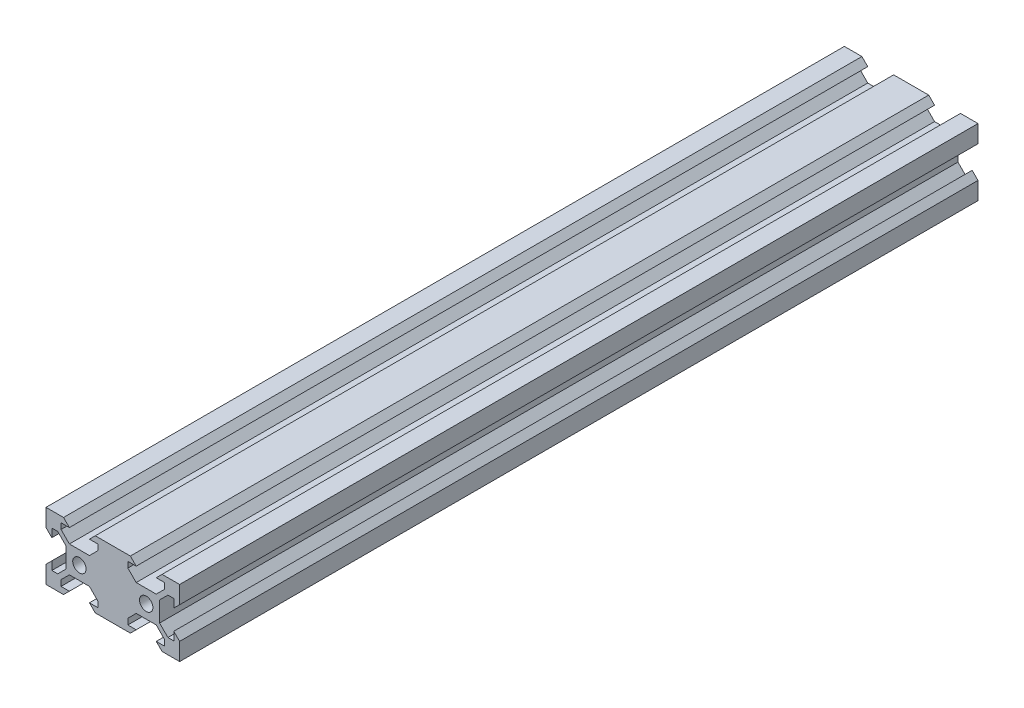
SolidWorks part; units mm, degrees
ref_plane "Alzado" through (0, 0, 0) normal (0, 0, 1) x (1, 0, 0)
ref_plane "Planta" through (0, 0, 0) normal (0, 1, 0) x (1, 0, 0)
ref_plane "Vista lateral" through (0, 0, 0) normal (1, 0, 0) x (0, 0, -1)
sketch "Croquis1" plane through (0, 0, 0) normal (0, 0, 1) x (1, 0, 0)
  line L0 (0, 10) -> (0, 4) construction
  line L1 (-10, 10) -> (10, 10)
  line L2 (-10, 10) -> (-10, -10)
  line L3 (-10, -10) -> (30, -10)
  line L4 (10, 10) -> (10, -10)
  line L5 (-10, 10) -> (10, -10) construction
  line L6 (-10, -10) -> (10, 10) construction
  line L7 (-3, 4) -> (3, 4)
  line L8 (4.75, 10) -> (3, 8.25)
  line L9 (3, 8.25) -> (5.5, 8.25)
  line L10 (5.5, 8.25) -> (5.5, 6.5)
  line L11 (5.5, 6.5) -> (3, 4)
  line L12 (4.75, 10) -> (-4.75, 10)
  line L13 (0, 10) -> (0, 4) construction
  line L14 (-4.75, 10) -> (-3, 8.25)
  line L15 (-3, 8.25) -> (-5.5, 8.25)
  line L16 (-5.5, 8.25) -> (-5.5, 6.5)
  line L17 (-5.5, 6.5) -> (-3, 4)
  line L18 (20, 10) -> (20, 4) construction
  line L19 (10, -4.75) -> (10, 4.75)
  line L20 (10, 4.75) -> (8.25, 3)
  line L21 (8.25, 3) -> (8.25, 5.5)
  line L22 (8.25, 5.5) -> (6.5, 5.5)
  line L23 (6.5, 5.5) -> (4, 3)
  line L24 (4, 3) -> (4, -3)
  line L25 (6.5, -5.5) -> (4, -3)
  line L26 (8.25, -5.5) -> (6.5, -5.5)
  line L27 (8.25, -3) -> (8.25, -5.5)
  line L28 (10, -4.75) -> (8.25, -3)
  line L29 (-4.75, -10) -> (4.75, -10)
  line L30 (4.75, -10) -> (3, -8.25)
  line L31 (3, -8.25) -> (5.5, -8.25)
  line L32 (5.5, -8.25) -> (5.5, -6.5)
  line L33 (5.5, -6.5) -> (3, -4)
  line L34 (3, -4) -> (-3, -4)
  line L35 (-5.5, -6.5) -> (-3, -4)
  line L36 (-5.5, -8.25) -> (-5.5, -6.5)
  line L37 (-3, -8.25) -> (-5.5, -8.25)
  line L38 (-4.75, -10) -> (-3, -8.25)
  line L39 (-10, 4.75) -> (-10, -4.75)
  line L40 (-10, -4.75) -> (-8.25, -3)
  line L41 (-8.25, -3) -> (-8.25, -5.5)
  line L42 (-8.25, -5.5) -> (-6.5, -5.5)
  line L43 (-6.5, -5.5) -> (-4, -3)
  line L44 (-4, -3) -> (-4, 3)
  line L45 (-6.5, 5.5) -> (-4, 3)
  line L46 (-8.25, 5.5) -> (-6.5, 5.5)
  line L47 (-8.25, 3) -> (-8.25, 5.5)
  line L48 (-10, 4.75) -> (-8.25, 3)
  line L49 (30, -10) -> (10, 10) construction
  line L50 (30, 10) -> (10, -10) construction
  line L51 (20, 10) -> (20, 4) construction
  line L52 (30, 4.75) -> (28.25, 3)
  line L53 (28.25, 3) -> (28.25, 5.5)
  line L54 (28.25, 5.5) -> (26.5, 5.5)
  line L55 (26.5, 5.5) -> (24, 3)
  line L56 (24, -3) -> (24, 3)
  line L57 (26.5, -5.5) -> (24, -3)
  line L58 (28.25, -5.5) -> (26.5, -5.5)
  line L59 (28.25, -3) -> (28.25, -5.5)
  line L60 (30, -4.75) -> (28.25, -3)
  line L61 (30, 4.75) -> (30, -4.75)
  line L62 (24.75, -10) -> (23, -8.25)
  line L63 (23, -8.25) -> (25.5, -8.25)
  line L64 (25.5, -8.25) -> (25.5, -6.5)
  line L65 (25.5, -6.5) -> (23, -4)
  line L66 (17, -4) -> (23, -4)
  line L67 (14.5, -6.5) -> (17, -4)
  line L68 (14.5, -8.25) -> (14.5, -6.5)
  line L69 (17, -8.25) -> (14.5, -8.25)
  line L70 (15.25, -10) -> (17, -8.25)
  line L71 (24.75, -10) -> (15.25, -10)
  line L72 (10, -4.75) -> (11.75, -3)
  line L73 (11.75, -3) -> (11.75, -5.5)
  line L74 (11.75, -5.5) -> (13.5, -5.5)
  line L75 (13.5, -5.5) -> (16, -3)
  line L76 (16, 3) -> (16, -3)
  line L77 (13.5, 5.5) -> (16, 3)
  line L78 (11.75, 5.5) -> (13.5, 5.5)
  line L79 (11.75, 3) -> (11.75, 5.5)
  line L80 (10, 4.75) -> (11.75, 3)
  line L81 (25.5, 6.5) -> (23, 4)
  line L82 (25.5, 8.25) -> (25.5, 6.5)
  line L83 (23, 8.25) -> (25.5, 8.25)
  line L84 (24.75, 10) -> (23, 8.25)
  line L85 (15.25, 10) -> (24.75, 10)
  line L86 (14.5, 6.5) -> (17, 4)
  line L87 (14.5, 8.25) -> (14.5, 6.5)
  line L88 (17, 8.25) -> (14.5, 8.25)
  line L89 (15.25, 10) -> (17, 8.25)
  line L90 (23, 4) -> (17, 4)
  line L91 (30, 10) -> (30, -10)
  line L92 (30, 10) -> (10, 10)
  circle A0 centre (0, 0) radius 2
  circle A1 centre (20, 0) radius 2
  point P0 (0, 0)
  point P17 (0, -4)
  point P55 (0, 0)
  point P98 (20, 0)
  point P99 (20, 0)
  dimension "D2" = 4
  dimension "D1" = 20
  dimension "D3" = 6
  dimension "D4" = 3
  dimension "D5" = 1.75
  dimension "D6" = 45
  dimension "D7" = 3
  dimension "D8" = 5.5
  dimension "D9" = 4
extrude "Saliente-Extruir1" add sketch "Croquis1" along normal blind 239 contours L2 L48 L47 L46 L45 L44 L43 L42 L41 L40 L3 L38 L37 L36 L35 L34 L33 L32 L31 L30 L4 L28 L27 L26 L25 L24 L23 L22 L21 L20 L1 L8 L9 L10 L11 L7 L17 L16 L15 L14 A0 | L91 L92 L84 L83 L82 L81 L90 L86 L87 L88 L89 L4 L80 L79 L78 L77 L76 L75 L74 L73 L72 L3 L70 L69 L68 L67 L66 L65 L64 L63 L62 L60 L59 L58 L57 L56 L55 L54 L53 L52 A1 | L80 L4 L72 L73 L74 L75 L76 L77 L78 L79 | L28 L4 L20 L21 L22 L23 L24 L25 L26 L27
